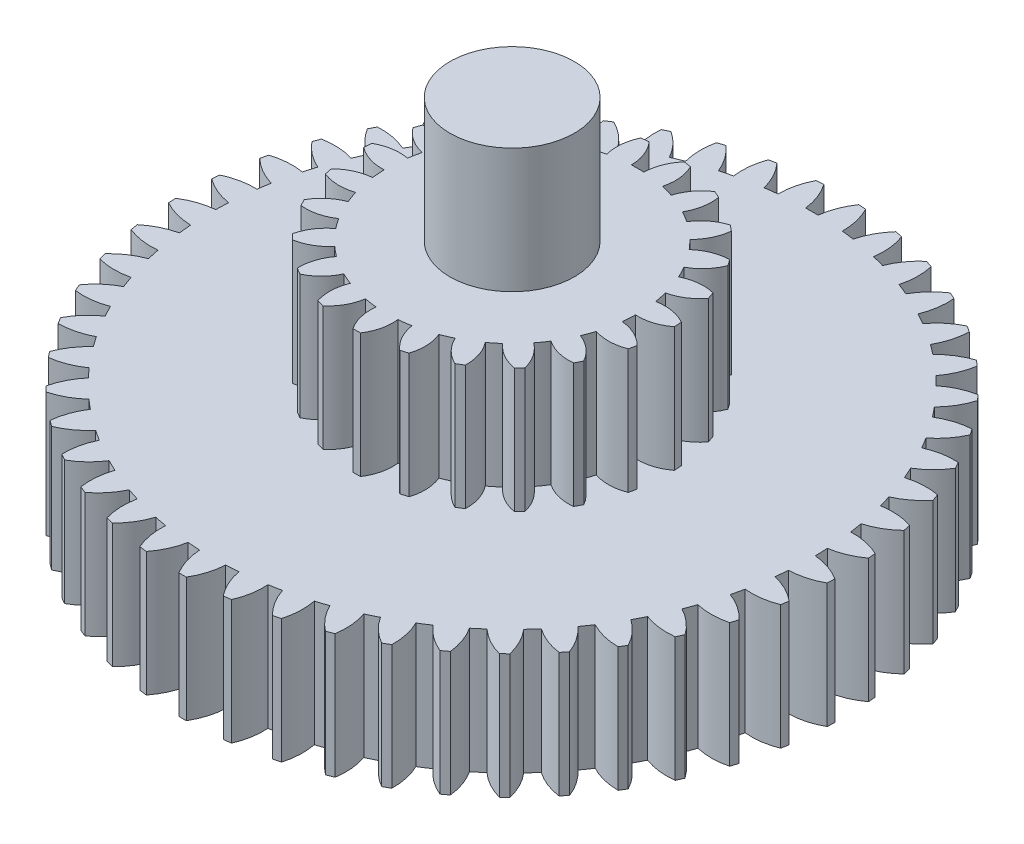
SolidWorks part; units mm, degrees
ref_plane "Front Plane" through (0, 0, 0) normal (0, 0, 1) x (1, 0, 0)
ref_plane "Top Plane" through (0, 0, 0) normal (0, 1, 0) x (1, 0, 0)
ref_plane "Right Plane" through (0, 0, 0) normal (1, 0, 0) x (0, 0, -1)
sketch "Sketch1" plane through (0, 0, 0) normal (0, 1, 0) x (1, 0, 0)
  line L0 (0, 0) -> (0, 2.41) construction
  arc A0 (-2.4765, 0.9432) -> (-2.4971, 0.8872) centre (0, 0) ccw
  arc A1 (-1.4011, 1.9609) -> (-1.4812, 1.9011) centre (0, 0) ccw
  arc A2 (0.05, 2.4095) -> (0.14, 2.6463) centre (0.5767, 2.3448) cw
  arc A3 (-0.05, 2.4095) -> (-0.14, 2.6463) centre (-0.5767, 2.3448) ccw
  arc A4 (0.3577, 2.3833) -> (0.4773, 2.6067) centre (0.8718, 2.2518) cw
  arc A5 (0.2585, 2.3961) -> (0.1996, 2.6425) centre (-0.2721, 2.3993) ccw
  arc A6 (0.6595, 2.318) -> (0.8067, 2.5242) centre (1.1526, 2.1219) cw
  arc A7 (0.5628, 2.3434) -> (0.5358, 2.5953) centre (0.0369, 2.4144) ccw
  arc A8 (0.9505, 2.2146) -> (1.1228, 2.4004) centre (1.4145, 1.957) cw
  arc A9 (0.8579, 2.2522) -> (0.8633, 2.5054) centre (0.3454, 2.3899) ccw
  arc A10 (1.2259, 2.0749) -> (1.4206, 2.2371) centre (1.6531, 1.7601) cw
  arc A11 (1.1388, 2.124) -> (1.1766, 2.3745) centre (0.6482, 2.3261) ccw
  arc A12 (1.4812, 1.9011) -> (1.695, 2.037) centre (1.8646, 1.5342) cw
  arc A13 (1.4011, 1.9609) -> (1.4706, 2.2045) centre (0.9403, 2.2241) ccw
  arc A14 (1.7122, 1.6961) -> (1.9416, 1.8036) centre (2.0455, 1.2832) cw
  arc A15 (1.6403, 1.7656) -> (1.7404, 1.9984) centre (1.217, 2.0856) ccw
  arc A16 (1.915, 1.4632) -> (2.1562, 1.5405) centre (2.1928, 1.0111) cw
  arc A17 (1.8526, 1.5414) -> (1.9817, 1.7594) centre (1.4737, 1.9129) ccw
  arc A18 (2.0864, 1.2063) -> (2.3355, 1.2521) centre (2.3041, 0.7224) cw
  arc A19 (2.0345, 1.2918) -> (2.1904, 1.4915) centre (1.7062, 1.7087) ccw
  arc A20 (2.2235, 0.9296) -> (2.4765, 0.9432) centre (2.3776, 0.4218) cw
  arc A21 (2.183, 1.021) -> (2.3631, 1.1992) centre (1.9107, 1.4765) ccw
  arc A22 (2.3241, 0.6376) -> (2.5768, 0.6187) centre (2.412, 0.1143) cw
  arc A23 (2.2957, 0.7335) -> (2.4971, 0.8872) centre (2.0838, 1.22) ccw
  arc A24 (2.3866, 0.3352) -> (2.6347, 0.2841) centre (2.4068, -0.1951) cw
  arc A25 (2.3706, 0.4339) -> (2.59, 0.5606) centre (2.2227, 0.9435) ccw
  arc A26 (2.4098, 0.0273) -> (2.6494, -0.0551) centre (2.3621, -0.5012) cw
  arc A27 (2.4066, 0.1272) -> (2.6405, 0.2247) centre (2.3251, 0.6516) ccw
  arc A28 (2.3935, -0.2811) -> (2.6206, -0.3935) centre (2.2786, -0.7992) cw
  arc A29 (2.4031, -0.1816) -> (2.6475, -0.1148) centre (2.3894, 0.3489) ccw
  arc A30 (2.3379, -0.5849) -> (2.5488, -0.7253) centre (2.1577, -1.084) cw
  arc A31 (2.3602, -0.4874) -> (2.6111, -0.4524) centre (2.4144, 0.0405) ccw
  arc A32 (2.244, -0.8791) -> (2.4351, -1.0453) centre (2.0014, -1.351) cw
  arc A33 (2.2785, -0.7852) -> (2.5318, -0.7826) centre (2.3997, -0.2686) ccw
  arc A34 (2.1131, -1.1588) -> (2.2815, -1.3481) centre (1.8122, -1.5959) cw
  arc A35 (2.1594, -1.0701) -> (2.411, -1.0999) centre (2.3457, -0.5733) ccw
  arc A36 (1.9476, -1.4195) -> (2.0903, -1.6288) centre (1.5932, -1.8145) cw
  arc A37 (2.0048, -1.3375) -> (2.2505, -1.3992) centre (2.2531, -0.8685) ccw
  arc A38 (1.7501, -1.6569) -> (1.8649, -1.8827) centre (1.3481, -2.0033) cw
  arc A39 (1.8173, -1.5829) -> (2.0531, -1.6755) centre (2.1235, -1.1495) ccw
  arc A40 (1.5238, -1.8671) -> (1.6088, -2.1058) centre (1.0809, -2.1593) cw
  arc A41 (1.6, -1.8023) -> (1.822, -1.9243) centre (1.9591, -1.4116) ccw
  arc A42 (1.2726, -2.0466) -> (1.3263, -2.2942) centre (0.7959, -2.2798) cw
  arc A43 (1.3564, -1.9921) -> (1.561, -2.1415) centre (1.7625, -1.6506) ccw
  arc A44 (1.0004, -2.1926) -> (1.0221, -2.445) centre (0.4978, -2.3628) cw
  arc A45 (1.0905, -2.1492) -> (1.2743, -2.3235) centre (1.537, -1.8624) ccw
  arc A46 (0.7118, -2.3025) -> (0.701, -2.5556) centre (0.1916, -2.4071) cw
  arc A47 (0.8067, -2.271) -> (0.9667, -2.4674) centre (1.2862, -2.0437) ccw
  arc A48 (0.4115, -2.3746) -> (0.3684, -2.6243) centre (-0.1178, -2.4118) cw
  arc A49 (0.5097, -2.3555) -> (0.6433, -2.5707) centre (1.0143, -2.1913) ccw
  arc A50 (0.1045, -2.4077) -> (0.0298, -2.6498) centre (-0.4253, -2.377) cw
  arc A51 (0.2043, -2.4013) -> (0.3093, -2.6319) centre (0.7257, -2.3031) ccw
  arc A52 (-0.2043, -2.4013) -> (-0.3093, -2.6319) centre (-0.7257, -2.3031) cw
  arc A53 (-0.1045, -2.4077) -> (-0.0298, -2.6498) centre (0.4253, -2.377) ccw
  arc A54 (-0.5097, -2.3555) -> (-0.6433, -2.5707) centre (-1.0143, -2.1913) cw
  arc A55 (-0.4115, -2.3746) -> (-0.3684, -2.6243) centre (0.1178, -2.4118) ccw
  arc A56 (-0.8067, -2.271) -> (-0.9667, -2.4674) centre (-1.2862, -2.0437) cw
  arc A57 (-0.7118, -2.3025) -> (-0.701, -2.5556) centre (-0.1916, -2.4071) ccw
  arc A58 (-1.0905, -2.1492) -> (-1.2743, -2.3235) centre (-1.537, -1.8624) cw
  arc A59 (-1.0004, -2.1926) -> (-1.0221, -2.445) centre (-0.4978, -2.3628) ccw
  arc A60 (-1.3564, -1.9921) -> (-1.561, -2.1415) centre (-1.7625, -1.6506) cw
  arc A61 (-1.2726, -2.0466) -> (-1.3263, -2.2942) centre (-0.7959, -2.2798) ccw
  arc A62 (-1.6, -1.8023) -> (-1.822, -1.9243) centre (-1.9591, -1.4116) cw
  arc A63 (-1.5238, -1.8671) -> (-1.6088, -2.1058) centre (-1.0809, -2.1593) ccw
  arc A64 (-1.8173, -1.5829) -> (-2.0531, -1.6755) centre (-2.1235, -1.1495) cw
  arc A65 (-1.7501, -1.6569) -> (-1.8649, -1.8827) centre (-1.3481, -2.0033) ccw
  arc A66 (-2.0048, -1.3375) -> (-2.2505, -1.3992) centre (-2.2531, -0.8685) cw
  arc A67 (-1.9476, -1.4195) -> (-2.0903, -1.6288) centre (-1.5932, -1.8145) ccw
  arc A68 (-2.1594, -1.0701) -> (-2.411, -1.0999) centre (-2.3457, -0.5733) cw
  arc A69 (-2.1131, -1.1588) -> (-2.2815, -1.3481) centre (-1.8122, -1.5959) ccw
  arc A70 (-2.2785, -0.7852) -> (-2.5318, -0.7826) centre (-2.3997, -0.2686) cw
  arc A71 (-2.244, -0.8791) -> (-2.4351, -1.0453) centre (-2.0014, -1.351) ccw
  arc A72 (-2.3602, -0.4874) -> (-2.6111, -0.4524) centre (-2.4144, 0.0405) cw
  arc A73 (-2.3379, -0.5849) -> (-2.5488, -0.7253) centre (-2.1577, -1.084) ccw
  arc A74 (-2.4031, -0.1816) -> (-2.6475, -0.1148) centre (-2.3894, 0.3489) cw
  arc A75 (-2.3935, -0.2811) -> (-2.6206, -0.3935) centre (-2.2786, -0.7992) ccw
  arc A76 (-2.4066, 0.1272) -> (-2.6405, 0.2247) centre (-2.3251, 0.6516) cw
  arc A77 (-2.4098, 0.0273) -> (-2.6494, -0.0551) centre (-2.3621, -0.5012) ccw
  arc A78 (-2.3706, 0.4339) -> (-2.59, 0.5606) centre (-2.2227, 0.9435) cw
  arc A79 (-2.3866, 0.3352) -> (-2.6347, 0.2841) centre (-2.4068, -0.1951) ccw
  arc A80 (-2.2957, 0.7335) -> (-2.4971, 0.8872) centre (-2.0838, 1.22) cw
  arc A81 (-2.3241, 0.6376) -> (-2.5768, 0.6187) centre (-2.412, 0.1143) ccw
  arc A82 (-2.183, 1.021) -> (-2.3631, 1.1992) centre (-1.9107, 1.4765) cw
  arc A83 (-2.2235, 0.9296) -> (-2.4765, 0.9432) centre (-2.3776, 0.4218) ccw
  arc A84 (-2.0345, 1.2918) -> (-2.1904, 1.4915) centre (-1.7062, 1.7087) cw
  arc A85 (-2.0864, 1.2063) -> (-2.3355, 1.2521) centre (-2.3041, 0.7224) ccw
  arc A86 (-1.8526, 1.5414) -> (-1.9817, 1.7594) centre (-1.4737, 1.9129) cw
  arc A87 (-1.915, 1.4632) -> (-2.1562, 1.5405) centre (-2.1928, 1.0111) ccw
  arc A88 (-1.6403, 1.7656) -> (-1.7404, 1.9984) centre (-1.217, 2.0856) cw
  arc A89 (-1.7122, 1.6961) -> (-1.9416, 1.8036) centre (-2.0455, 1.2832) ccw
  arc A90 (-1.4011, 1.9609) -> (-1.4706, 2.2045) centre (-0.9403, 2.2241) cw
  arc A91 (-1.4812, 1.9011) -> (-1.695, 2.037) centre (-1.8646, 1.5342) ccw
  arc A92 (-1.1388, 2.124) -> (-1.1766, 2.3745) centre (-0.6482, 2.3261) cw
  arc A93 (-1.2259, 2.0749) -> (-1.4206, 2.2371) centre (-1.6531, 1.7601) ccw
  arc A94 (-2.5768, 0.6187) -> (-2.59, 0.5606) centre (0, 0) ccw
  arc A95 (-2.6347, 0.2841) -> (-2.6405, 0.2247) centre (0, 0) ccw
  arc A96 (-2.6494, -0.0551) -> (-2.6475, -0.1148) centre (0, 0) ccw
  arc A97 (-2.3355, 1.2521) -> (-2.3631, 1.1992) centre (0, 0) ccw
  arc A98 (-2.1562, 1.5405) -> (-2.1904, 1.4915) centre (0, 0) ccw
  arc A99 (-1.9416, 1.8036) -> (-1.9817, 1.7594) centre (0, 0) ccw
  arc A100 (-1.695, 2.037) -> (-1.7404, 1.9984) centre (0, 0) ccw
  arc A101 (-1.4206, 2.2371) -> (-1.4706, 2.2045) centre (0, 0) ccw
  arc A102 (-0.14, 2.6463) -> (-0.1996, 2.6425) centre (0, 0) ccw
  arc A103 (0.1996, 2.6425) -> (0.14, 2.6463) centre (0, 0) ccw
  arc A104 (0.5358, 2.5953) -> (0.4773, 2.6067) centre (0, 0) ccw
  arc A105 (0.8633, 2.5054) -> (0.8067, 2.5242) centre (0, 0) ccw
  arc A106 (1.1766, 2.3745) -> (1.1228, 2.4004) centre (0, 0) ccw
  arc A107 (1.4706, 2.2045) -> (1.4206, 2.2371) centre (0, 0) ccw
  arc A108 (1.7404, 1.9984) -> (1.695, 2.037) centre (0, 0) ccw
  arc A109 (1.9817, 1.7594) -> (1.9416, 1.8036) centre (0, 0) ccw
  arc A110 (2.1904, 1.4915) -> (2.1562, 1.5405) centre (0, 0) ccw
  arc A111 (2.3631, 1.1992) -> (2.3355, 1.2521) centre (0, 0) ccw
  arc A112 (2.4971, 0.8872) -> (2.4765, 0.9432) centre (0, 0) ccw
  arc A113 (2.59, 0.5606) -> (2.5768, 0.6187) centre (0, 0) ccw
  arc A114 (2.6405, 0.2247) -> (2.6347, 0.2841) centre (0, 0) ccw
  arc A115 (2.6475, -0.1148) -> (2.6494, -0.0551) centre (0, 0) ccw
  arc A116 (2.6111, -0.4524) -> (2.6206, -0.3935) centre (0, 0) ccw
  arc A117 (2.5318, -0.7826) -> (2.5488, -0.7253) centre (0, 0) ccw
  arc A118 (2.411, -1.0999) -> (2.4351, -1.0453) centre (0, 0) ccw
  arc A119 (2.0531, -1.6755) -> (2.0903, -1.6288) centre (0, 0) ccw
  arc A120 (2.2505, -1.3992) -> (2.2815, -1.3481) centre (0, 0) ccw
  arc A121 (1.822, -1.9243) -> (1.8649, -1.8827) centre (0, 0) ccw
  arc A122 (1.561, -2.1415) -> (1.6088, -2.1058) centre (0, 0) ccw
  arc A123 (1.2743, -2.3235) -> (1.3263, -2.2942) centre (0, 0) ccw
  arc A124 (0.9667, -2.4674) -> (1.0221, -2.445) centre (0, 0) ccw
  arc A125 (0.6433, -2.5707) -> (0.701, -2.5556) centre (0, 0) ccw
  arc A126 (0.3093, -2.6319) -> (0.3684, -2.6243) centre (0, 0) ccw
  arc A127 (-0.0298, -2.6498) -> (0.0298, -2.6498) centre (0, 0) ccw
  arc A128 (-0.3684, -2.6243) -> (-0.3093, -2.6319) centre (0, 0) ccw
  arc A129 (-0.701, -2.5556) -> (-0.6433, -2.5707) centre (0, 0) ccw
  arc A130 (-1.0221, -2.445) -> (-0.9667, -2.4674) centre (0, 0) ccw
  arc A131 (-1.3263, -2.2942) -> (-1.2743, -2.3235) centre (0, 0) ccw
  arc A132 (-1.6088, -2.1058) -> (-1.561, -2.1415) centre (0, 0) ccw
  arc A133 (-1.8649, -1.8827) -> (-1.822, -1.9243) centre (0, 0) ccw
  arc A134 (-2.2815, -1.3481) -> (-2.2505, -1.3992) centre (0, 0) ccw
  arc A135 (-2.0903, -1.6288) -> (-2.0531, -1.6755) centre (0, 0) ccw
  arc A136 (-2.4351, -1.0453) -> (-2.411, -1.0999) centre (0, 0) ccw
  arc A137 (-2.5488, -0.7253) -> (-2.5318, -0.7826) centre (0, 0) ccw
  arc A138 (-2.6206, -0.3935) -> (-2.6111, -0.4524) centre (0, 0) ccw
  arc A139 (-1.6403, 1.7656) -> (-1.7122, 1.6961) centre (0, 0) ccw
  arc A140 (-1.8526, 1.5414) -> (-1.915, 1.4632) centre (0, 0) ccw
  arc A141 (-2.0345, 1.2918) -> (-2.0864, 1.2063) centre (0, 0) ccw
  arc A142 (-2.183, 1.021) -> (-2.2235, 0.9296) centre (0, 0) ccw
  arc A143 (-2.2957, 0.7335) -> (-2.3241, 0.6376) centre (0, 0) ccw
  arc A144 (-2.3706, 0.4339) -> (-2.3866, 0.3352) centre (0, 0) ccw
  arc A145 (-2.4066, 0.1272) -> (-2.4098, 0.0273) centre (0, 0) ccw
  arc A146 (-2.3602, -0.4874) -> (-2.3379, -0.5849) centre (0, 0) ccw
  arc A147 (-2.2785, -0.7852) -> (-2.244, -0.8791) centre (0, 0) ccw
  arc A148 (-2.1594, -1.0701) -> (-2.1131, -1.1588) centre (0, 0) ccw
  arc A149 (-2.0048, -1.3375) -> (-1.9476, -1.4195) centre (0, 0) ccw
  arc A150 (-1.8173, -1.5829) -> (-1.7501, -1.6569) centre (0, 0) ccw
  arc A151 (-1.6, -1.8023) -> (-1.5238, -1.8671) centre (0, 0) ccw
  arc A152 (-1.0905, -2.1492) -> (-1.0004, -2.1926) centre (0, 0) ccw
  arc A153 (-0.8067, -2.271) -> (-0.7118, -2.3025) centre (0, 0) ccw
  arc A154 (-0.5097, -2.3555) -> (-0.4115, -2.3746) centre (0, 0) ccw
  arc A155 (-0.2043, -2.4013) -> (-0.1045, -2.4077) centre (0, 0) ccw
  arc A156 (0.1045, -2.4077) -> (0.2043, -2.4013) centre (0, 0) ccw
  arc A157 (0.4115, -2.3746) -> (0.5097, -2.3555) centre (0, 0) ccw
  arc A158 (0.7118, -2.3025) -> (0.8067, -2.271) centre (0, 0) ccw
  arc A159 (1.0004, -2.1926) -> (1.0905, -2.1492) centre (0, 0) ccw
  arc A160 (1.2726, -2.0466) -> (1.3564, -1.9921) centre (0, 0) ccw
  arc A161 (1.5238, -1.8671) -> (1.6, -1.8023) centre (0, 0) ccw
  arc A162 (1.7501, -1.6569) -> (1.8173, -1.5829) centre (0, 0) ccw
  arc A163 (1.9476, -1.4195) -> (2.0048, -1.3375) centre (0, 0) ccw
  arc A164 (2.1131, -1.1588) -> (2.1594, -1.0701) centre (0, 0) ccw
  arc A165 (2.244, -0.8791) -> (2.2785, -0.7852) centre (0, 0) ccw
  arc A166 (2.3379, -0.5849) -> (2.3602, -0.4874) centre (0, 0) ccw
  arc A167 (2.3935, -0.2811) -> (2.4031, -0.1816) centre (0, 0) ccw
  arc A168 (2.4098, 0.0273) -> (2.4066, 0.1272) centre (0, 0) ccw
  arc A169 (2.3866, 0.3352) -> (2.3706, 0.4339) centre (0, 0) ccw
  arc A170 (2.3241, 0.6376) -> (2.2957, 0.7335) centre (0, 0) ccw
  arc A171 (2.2235, 0.9296) -> (2.183, 1.021) centre (0, 0) ccw
  arc A172 (2.0864, 1.2063) -> (2.0345, 1.2918) centre (0, 0) ccw
  arc A173 (1.915, 1.4632) -> (1.8526, 1.5414) centre (0, 0) ccw
  arc A174 (1.7122, 1.6961) -> (1.6403, 1.7656) centre (0, 0) ccw
  arc A175 (1.4812, 1.9011) -> (1.4011, 1.9609) centre (0, 0) ccw
  arc A176 (1.2259, 2.0749) -> (1.1388, 2.124) centre (0, 0) ccw
  arc A177 (0.9505, 2.2146) -> (0.8579, 2.2522) centre (0, 0) ccw
  arc A178 (0.6595, 2.318) -> (0.5628, 2.3434) centre (0, 0) ccw
  arc A179 (0.3577, 2.3833) -> (0.2585, 2.3961) centre (0, 0) ccw
  arc A180 (0.05, 2.4095) -> (-0.05, 2.4095) centre (0, 0) ccw
  arc A181 (-1.1388, 2.124) -> (-1.2259, 2.0749) centre (0, 0) ccw
  arc A182 (-1.3564, -1.9921) -> (-1.2726, -2.0466) centre (0, 0) ccw
  arc A183 (-2.4031, -0.1816) -> (-2.3935, -0.2811) centre (0, 0) ccw
  arc A184 (-0.8579, 2.2522) -> (-0.8633, 2.5054) centre (-0.3454, 2.3899) cw
  arc A185 (-0.9505, 2.2146) -> (-1.1228, 2.4004) centre (-1.4145, 1.957) ccw
  arc A186 (-0.5628, 2.3434) -> (-0.5358, 2.5953) centre (-0.0369, 2.4144) cw
  arc A187 (-0.6595, 2.318) -> (-0.8067, 2.5242) centre (-1.1526, 2.1219) ccw
  arc A188 (-1.1228, 2.4004) -> (-1.1766, 2.3745) centre (0, 0) ccw
  arc A189 (-0.8067, 2.5242) -> (-0.8633, 2.5054) centre (0, 0) ccw
  arc A190 (-0.9505, 2.2146) -> (-0.8579, 2.2522) centre (0, 0) cw
  arc A191 (-0.6595, 2.318) -> (-0.5628, 2.3434) centre (0, 0) cw
  arc A192 (-0.2585, 2.3961) -> (-0.1996, 2.6425) centre (0.2721, 2.3993) cw
  arc A193 (-0.3577, 2.3833) -> (-0.4773, 2.6067) centre (-0.8718, 2.2518) ccw
  arc A194 (-0.4773, 2.6067) -> (-0.5358, 2.5953) centre (0, 0) ccw
  arc A195 (-0.3577, 2.3833) -> (-0.2585, 2.3961) centre (0, 0) cw
  point P4 (0, 2.41)
  point P5 (0, 2.65)
  point P309 (0, 0)
  dimension "D1" = 5.3
  dimension "D2" = 0.24
  dimension "D3" = 0.05
  dimension "D4" = 0.14
  dimension "D5" = 49
extrude "Boss-Extrude1" add sketch "Sketch1" along normal blind 1 contours A92 A181 A93 A101 A90 A1 A91 A100 A88 A139 A89 A99 A86 A140 A87 A98 A84 A141 A85 A97 A82 A142 A83 A0 A80 A143 A81 A94 A78 A144 A79 A95 A76 A145 A75 A138 A72 A146 A73 A137 A70 A147 A71 A136 A68 A148 A69 A134 A66
sketch "Sketch2" plane through (0, 1, 0) normal (0, 1, 0) x (1, 0, 0)
  circle A0 centre (0, 0) radius 0.5
  dimension "D1" = 1
extrude "Boss-Extrude2" add sketch "Sketch2" along normal blind 2 and the other way blind 2
sketch "Sketch3" plane through (0, 1, 0) normal (0, 1, 0) x (1, 0, 0)
  line L1 (0, 1.25) -> (0, 1.6924) construction
  arc A0 (-1.1673, 0.4472) -> (-1.1877, 0.3898) centre (0, 0) ccw
  arc A1 (-0.4814, 0.8879) -> (-0.5669, 0.8359) centre (0, 0) ccw
  arc A2 (0.05, 1.0088) -> (0.14, 1.2421) centre (0.4138, 1.0025) cw
  arc A3 (-0.05, 1.0088) -> (-0.14, 1.2421) centre (-0.4138, 1.0025) ccw
  arc A4 (0.3203, 0.9579) -> (0.4699, 1.1583) centre (0.6689, 0.8537) cw
  arc A5 (0.224, 0.9848) -> (0.2003, 1.2338) centre (-0.1279, 1.077) ccw
  arc A6 (0.5669, 0.8359) -> (0.765, 0.9886) centre (0.8744, 0.6416) cw
  arc A7 (0.4814, 0.8879) -> (0.5258, 1.134) centre (0.1674, 1.0716) ccw
  arc A8 (0.7714, 0.652) -> (1.0034, 0.7455) centre (1.0151, 0.3819) cw
  arc A9 (0.7031, 0.7251) -> (0.8122, 0.9501) centre (0.4503, 0.9867) ccw
  arc A10 (0.9187, 0.4197) -> (1.1673, 0.4472) centre (1.0805, 0.0939) cw
  arc A11 (0.8727, 0.5085) -> (1.0385, 0.6958) centre (0.6998, 0.8286) ccw
  arc A12 (0.9978, 0.1563) -> (1.2446, 0.1156) centre (1.0657, -0.2011) cw
  arc A13 (0.9775, 0.2542) -> (1.1877, 0.3898) centre (0.8974, 0.6091) ccw
  arc A14 (1.003, -0.1187) -> (1.2297, -0.2244) centre (0.9719, -0.4812) cw
  arc A15 (1.0098, -0.019) -> (1.2488, 0.0549) centre (1.0284, 0.3444) ccw
  arc A16 (0.9338, -0.3849) -> (1.1235, -0.5479) centre (0.8061, -0.7256) cw
  arc A17 (0.9673, -0.2907) -> (1.2173, -0.284) centre (1.0832, 0.0541) ccw
  arc A18 (0.7953, -0.6226) -> (0.9341, -0.8307) centre (0.5804, -0.9162) cw
  arc A19 (0.853, -0.5409) -> (1.0955, -0.6019) centre (1.0576, -0.2401) ccw
  arc A20 (0.5978, -0.8141) -> (0.6753, -1.0519) centre (0.3117, -1.0388) cw
  arc A21 (0.6754, -0.751) -> (0.8925, -0.8752) centre (0.9536, -0.5166) ccw
  arc A22 (0.356, -0.9452) -> (0.3665, -1.1951) centre (0.0199, -1.0844) cw
  arc A23 (0.4478, -0.9053) -> (0.6233, -1.0835) centre (0.7789, -0.7547) ccw
  arc A24 (0.0878, -1.0062) -> (0.0304, -1.2496) centre (-0.2734, -1.0495) cw
  arc A25 (0.1869, -0.9926) -> (0.3078, -1.2115) centre (0.5464, -0.9368) ccw
  arc A26 (-0.1869, -0.9926) -> (-0.3078, -1.2115) centre (-0.5464, -0.9368) cw
  arc A27 (-0.0878, -1.0062) -> (-0.0304, -1.2496) centre (0.2734, -1.0495) ccw
  arc A28 (-0.4478, -0.9053) -> (-0.6233, -1.0835) centre (-0.7789, -0.7547) cw
  arc A29 (-0.356, -0.9452) -> (-0.3665, -1.1951) centre (-0.0199, -1.0844) ccw
  arc A30 (-0.6754, -0.751) -> (-0.8925, -0.8752) centre (-0.9536, -0.5166) cw
  arc A31 (-0.5978, -0.8141) -> (-0.6753, -1.0519) centre (-0.3117, -1.0388) ccw
  arc A32 (-0.853, -0.5409) -> (-1.0955, -0.6019) centre (-1.0576, -0.2401) cw
  arc A33 (-0.7953, -0.6226) -> (-0.9341, -0.8307) centre (-0.5804, -0.9162) ccw
  arc A34 (-0.9673, -0.2907) -> (-1.2173, -0.284) centre (-1.0832, 0.0541) cw
  arc A35 (-0.9338, -0.3849) -> (-1.1235, -0.5479) centre (-0.8061, -0.7256) ccw
  arc A36 (-1.0098, -0.019) -> (-1.2488, 0.0549) centre (-1.0284, 0.3444) cw
  arc A37 (-1.003, -0.1187) -> (-1.2297, -0.2244) centre (-0.9719, -0.4812) ccw
  arc A38 (-0.9775, 0.2542) -> (-1.1877, 0.3898) centre (-0.8974, 0.6091) cw
  arc A39 (-0.9978, 0.1563) -> (-1.2446, 0.1156) centre (-1.0657, -0.2011) ccw
  arc A40 (-0.8727, 0.5085) -> (-1.0385, 0.6958) centre (-0.6998, 0.8286) cw
  arc A41 (-0.9187, 0.4197) -> (-1.1673, 0.4472) centre (-1.0805, 0.0939) ccw
  arc A42 (-0.7031, 0.7251) -> (-0.8122, 0.9501) centre (-0.4503, 0.9867) cw
  arc A43 (-0.7714, 0.652) -> (-1.0034, 0.7455) centre (-1.0151, 0.3819) ccw
  arc A44 (-0.4814, 0.8879) -> (-0.5258, 1.134) centre (-0.1674, 1.0716) cw
  arc A45 (-0.5669, 0.8359) -> (-0.765, 0.9886) centre (-0.8744, 0.6416) ccw
  arc A46 (-0.224, 0.9848) -> (-0.2003, 1.2338) centre (0.1279, 1.077) cw
  arc A47 (-0.3203, 0.9579) -> (-0.4699, 1.1583) centre (-0.6689, 0.8537) ccw
  arc A48 (-1.0034, 0.7455) -> (-1.0385, 0.6958) centre (0, 0) ccw
  arc A49 (-0.765, 0.9886) -> (-0.8122, 0.9501) centre (0, 0) ccw
  arc A50 (-0.4699, 1.1583) -> (-0.5258, 1.134) centre (0, 0) ccw
  arc A51 (-0.14, 1.2421) -> (-0.2003, 1.2338) centre (0, 0) ccw
  arc A52 (0.2003, 1.2338) -> (0.14, 1.2421) centre (0, 0) ccw
  arc A53 (0.5258, 1.134) -> (0.4699, 1.1583) centre (0, 0) ccw
  arc A54 (0.8122, 0.9501) -> (0.765, 0.9886) centre (0, 0) ccw
  arc A55 (1.0385, 0.6958) -> (1.0034, 0.7455) centre (0, 0) ccw
  arc A56 (1.1877, 0.3898) -> (1.1673, 0.4472) centre (0, 0) ccw
  arc A57 (1.2488, 0.0549) -> (1.2446, 0.1156) centre (0, 0) ccw
  arc A58 (-1.2446, 0.1156) -> (-1.2488, 0.0549) centre (0, 0) ccw
  arc A59 (-1.2297, -0.2244) -> (-1.2173, -0.284) centre (0, 0) ccw
  arc A60 (-1.1235, -0.5479) -> (-1.0955, -0.6019) centre (0, 0) ccw
  arc A61 (-0.9341, -0.8307) -> (-0.8925, -0.8752) centre (0, 0) ccw
  arc A62 (-0.6753, -1.0519) -> (-0.6233, -1.0835) centre (0, 0) ccw
  arc A63 (-0.3665, -1.1951) -> (-0.3078, -1.2115) centre (0, 0) ccw
  arc A64 (-0.0304, -1.2496) -> (0.0304, -1.2496) centre (0, 0) ccw
  arc A65 (0.3078, -1.2115) -> (0.3665, -1.1951) centre (0, 0) ccw
  arc A66 (0.6233, -1.0835) -> (0.6753, -1.0519) centre (0, 0) ccw
  arc A67 (0.8925, -0.8752) -> (0.9341, -0.8307) centre (0, 0) ccw
  arc A68 (1.0955, -0.6019) -> (1.1235, -0.5479) centre (0, 0) ccw
  arc A69 (1.2173, -0.284) -> (1.2297, -0.2244) centre (0, 0) ccw
  arc A70 (-0.7031, 0.7251) -> (-0.7714, 0.652) centre (0, 0) ccw
  arc A71 (-0.8727, 0.5085) -> (-0.9187, 0.4197) centre (0, 0) ccw
  arc A72 (-0.9775, 0.2542) -> (-0.9978, 0.1563) centre (0, 0) ccw
  arc A73 (-1.0098, -0.019) -> (-1.003, -0.1187) centre (0, 0) ccw
  arc A74 (-0.9673, -0.2907) -> (-0.9338, -0.3849) centre (0, 0) ccw
  arc A75 (-0.853, -0.5409) -> (-0.7953, -0.6226) centre (0, 0) ccw
  arc A76 (-0.6754, -0.751) -> (-0.5978, -0.8141) centre (0, 0) ccw
  arc A77 (-0.4478, -0.9053) -> (-0.356, -0.9452) centre (0, 0) ccw
  arc A78 (-0.1869, -0.9926) -> (-0.0878, -1.0062) centre (0, 0) ccw
  arc A79 (0.0878, -1.0062) -> (0.1869, -0.9926) centre (0, 0) ccw
  arc A80 (0.356, -0.9452) -> (0.4478, -0.9053) centre (0, 0) ccw
  arc A81 (0.5978, -0.8141) -> (0.6754, -0.751) centre (0, 0) ccw
  arc A82 (0.7953, -0.6226) -> (0.853, -0.5409) centre (0, 0) ccw
  arc A83 (0.9338, -0.3849) -> (0.9673, -0.2907) centre (0, 0) ccw
  arc A84 (1.003, -0.1187) -> (1.0098, -0.019) centre (0, 0) ccw
  arc A85 (0.9978, 0.1563) -> (0.9775, 0.2542) centre (0, 0) ccw
  arc A86 (0.9187, 0.4197) -> (0.8727, 0.5085) centre (0, 0) ccw
  arc A87 (0.7714, 0.652) -> (0.7031, 0.7251) centre (0, 0) ccw
  arc A88 (0.5669, 0.8359) -> (0.4814, 0.8879) centre (0, 0) ccw
  arc A89 (0.3203, 0.9579) -> (0.224, 0.9848) centre (0, 0) ccw
  arc A90 (0.05, 1.0088) -> (-0.05, 1.0088) centre (0, 0) ccw
  arc A91 (-0.224, 0.9848) -> (-0.3203, 0.9579) centre (0, 0) ccw
  point P4 (0, 1.25)
  point P5 (0, 1.01)
  point P148 (0, 0)
  dimension "D1" = 2.5
  dimension "D2" = 0.24
  dimension "D5" = 23
extrude "Boss-Extrude3" add sketch "Sketch3" along normal blind 1
